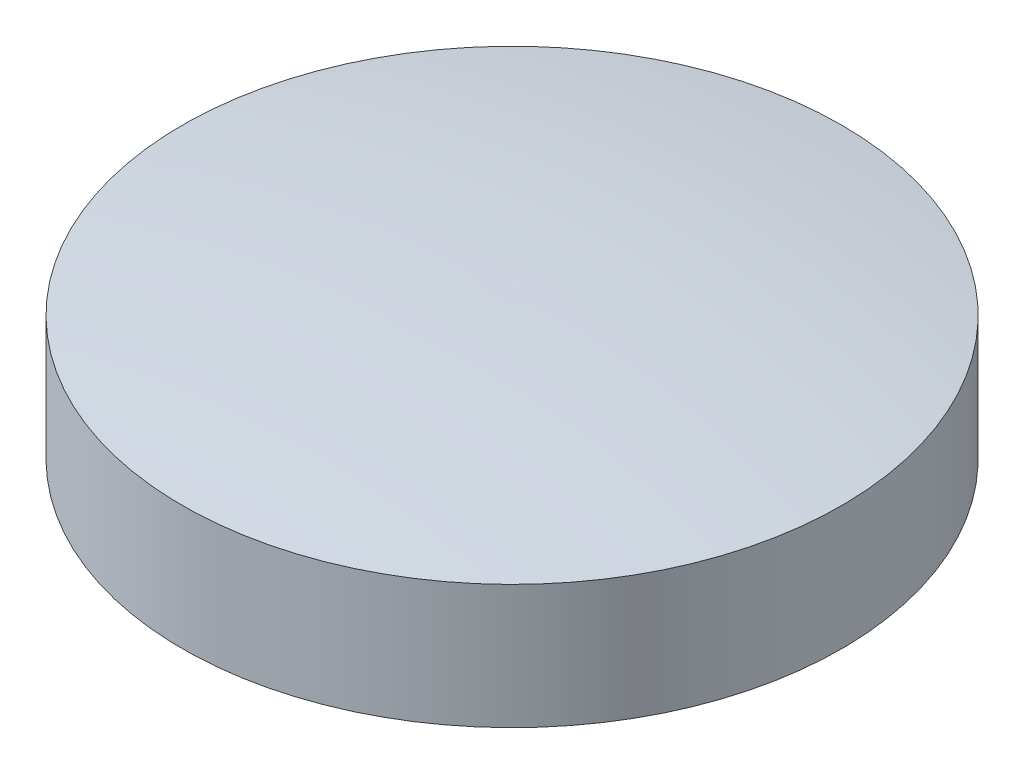
SolidWorks part; units mm, degrees
material "Glas"
ref_plane "Front" through (0, 0, 0) normal (0, 0, 1) x (1, 0, 0)
ref_plane "Top" through (0, 0, 0) normal (0, 1, 0) x (1, 0, 0)
ref_plane "Right" through (0, 0, 0) normal (1, 0, 0) x (0, 0, -1)
sketch "Skizze3" plane through (0, 0, 0) normal (1, 0, 0) x (0, 0, -1)
  line L0 (0, 0) -> (0, 14.7875) construction
  line L1 (0, 0) -> (25.5, 0)
  line L2 (25.5, 0) -> (25.5, 9.6)
  line L4 (0, 11.5159) -> (0, 0)
  arc A0 (25.5, 9.6) -> (0, 11.5159) centre (1.0338, -145.3851) ccw
  dimension "D1" = 51
  dimension "D2" = 9.6
revolve "Rotation1" add sketch "Skizze3" angle 360 about L0
